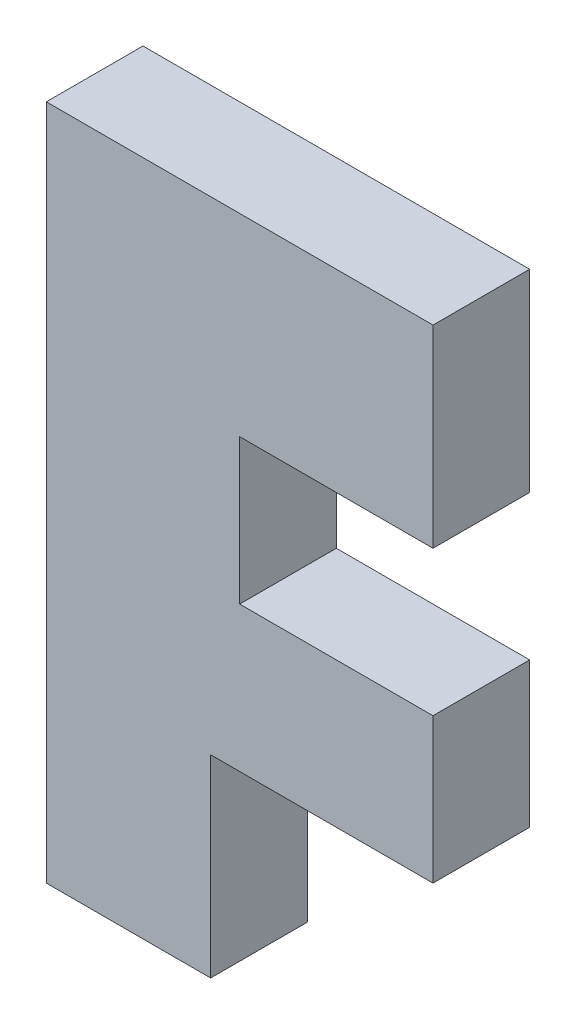
SolidWorks part; units mm, degrees
ref_plane "Front Plane" through (0, 0, 0) normal (0, 0, 1) x (1, 0, 0)
ref_plane "Top Plane" through (0, 0, 0) normal (0, 1, 0) x (1, 0, 0)
ref_plane "Right Plane" through (0, 0, 0) normal (1, 0, 0) x (0, 0, -1)
sketch "Sketch1" plane through (0, 0, 0) normal (0, 0, 1) x (1, 0, 0)
  line L0 (0, 0) -> (0, 88.9)
  line L1 (0, 88.9) -> (50.8, 88.9)
  line L2 (50.8, 88.9) -> (50.8, 63.5)
  line L3 (50.8, 63.5) -> (25.4, 63.5)
  line L4 (25.4, 63.5) -> (25.4, 44.45)
  line L5 (25.4, 44.45) -> (50.8, 44.45)
  line L6 (50.8, 44.45) -> (50.8, 25.4)
  line L7 (0, 0) -> (21.59, 0)
  line L9 (21.59, 25.4) -> (50.8, 25.4)
  line L10 (21.59, 0) -> (21.59, 25.4)
  dimension "D1" = 88.9
  dimension "D2" = 50.8
  dimension "D3" = 25.4
  dimension "D5" = 63.5
  dimension "D6" = 25.4
  dimension "D7" = 19.05
  dimension "D9" = 21.59
  dimension "D10" = 25.4
extrude "Boss-Extrude1" add sketch "Sketch1" along normal blind 12.7 contours L10 L9 L6 L5 L4 L3 L2 L1 L0 L7
